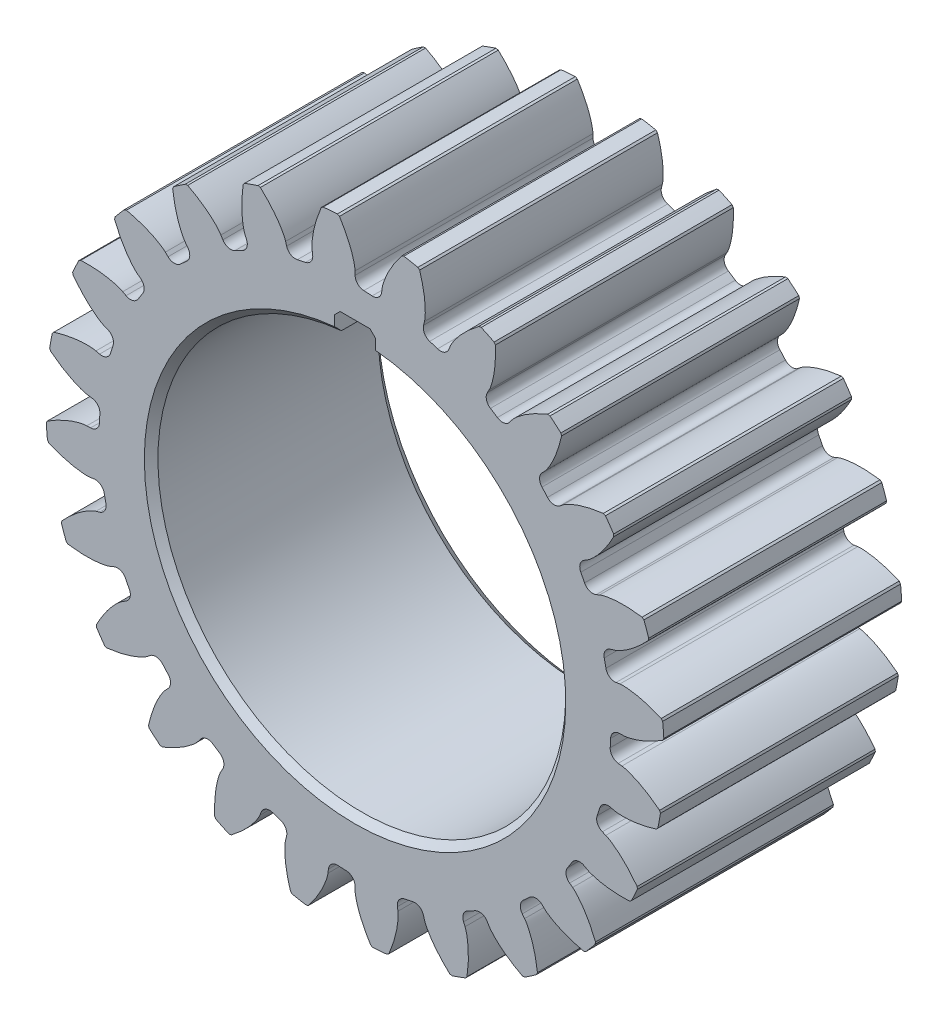
SolidWorks part; units mm, degrees
material "1.6587 (18CrNiMo7-6)"
ref_plane "Front Plane" through (0, 0, 0) normal (0, 0, 1) x (1, 0, 0)
ref_plane "Top Plane" through (0, 0, 0) normal (0, 1, 0) x (1, 0, 0)
ref_plane "Right Plane" through (0, 0, 0) normal (1, 0, 0) x (0, 0, -1)
sketch "Sketch1" plane through (0, 0, 0) normal (0, 0, 1) x (1, 0, 0)
  circle A0 centre (0, 0) radius 42 construction
  circle A1 centre (0, 0) radius 37.625
  dimension "D1" = 84
  dimension "D2" = 4.375
extrude "Boss-Extrude1" add sketch "Sketch1" along normal blind 35
sketch "Sketch2" plane through (0, 0, 0) normal (0, 0, 1) x (1, 0, 0)
  line L0 (39.4671, 0) -> (38.9123, -0.0082)
  line L1 (0, 0) -> (41.9953, 0.626) construction
  line L2 (0, 0) -> (57.5048, 4.6307) construction
  line L3 (38.9585, 6.3154) -> (38.4096, 6.2348)
  circle A0 centre (0, 0) radius 42 construction
  circle A1 centre (0, 0) radius 37.625 construction
  arc A2 (37.6028, -1.2924) -> (36.9114, 7.2929) centre (0, 0) ccw
  arc A3 (45.4365, 2.4027) -> (45.2355, 4.899) centre (0, 0) ccw
  arc A4 (38.9123, -0.0082) -> (37.6028, -1.2924) centre (38.932, -1.3381) ccw
  arc A5 (38.4096, 6.2348) -> (36.9114, 7.2929) centre (38.2162, 7.5506) cw
  circle A6 centre (0, 0) radius 45.5 construction
  spline S0 degree 4 poles (39.4671, 0) (39.4814, 0.0002) (39.5215, 0.0015) (39.5972, 0.0064) (39.7206, 0.0182) (39.8775, 0.0385) (40.0797, 0.071) (40.3172, 0.1173) (40.5771, 0.1764) (40.8586, 0.2496) (41.1382, 0.3305) (41.4158, 0.4184) (41.691, 0.5126) (42.0229, 0.6344) (42.4185, 0.7911) (42.8771, 0.9898) (43.3926, 1.2333) (43.9124, 1.5007) (44.4193, 1.7795) (44.9256, 2.0792) (45.4112, 2.3818) (45.9092, 2.7142) (46.3655, 3.0302) (46.869, 3.4039) (47.2732, 3.7113) (47.7975, 4.1375) (48.1046, 4.3953) (48.4608, 4.7041) (48.6173, 4.845) (48.7137, 4.9316) knots 0 0 0 0 0 0.005377 0.015084 0.028532 0.04661 0.064855 0.092111 0.119476 0.146842 0.174209 0.201575 0.228941 0.256307 0.307035 0.361767 0.4165 0.471232 0.525964 0.580697 0.635429 0.690161 0.744894 0.799626 0.854358 0.909091 0.954545 1 1 1 1 1 construction
  spline S1 degree 4 poles (39.4671, 0) (39.4814, 0.0002) (39.5215, 0.0015) (39.5972, 0.0064) (39.7206, 0.0182) (39.8775, 0.0385) (40.0797, 0.071) (40.3172, 0.1173) (40.5771, 0.1764) (40.8586, 0.2496) (41.1382, 0.3305) (41.4158, 0.4184) (41.691, 0.5126) (42.0229, 0.6344) (42.4185, 0.7911) (42.8771, 0.9898) (43.3926, 1.2333) (43.9124, 1.5007) (44.4193, 1.7795) (44.8682, 2.0452) (45.1794, 2.2376) (45.3694, 2.3592) (45.4365, 2.4027) knots 0 0 0 0 0 0.005377 0.015084 0.028532 0.04661 0.064855 0.092111 0.119476 0.146842 0.174209 0.201575 0.228941 0.256307 0.307035 0.361767 0.4165 0.471232 0.525964 0.580697 0.61062 0.61062 0.61062 0.61062 0.61062
  spline S2 degree 4 poles (38.9585, 6.3154) (38.9727, 6.3175) (39.0125, 6.3227) (39.088, 6.3299) (39.2117, 6.3381) (39.3698, 6.3431) (39.5746, 6.3433) (39.8164, 6.3357) (40.0824, 6.319) (40.372, 6.2918) (40.6609, 6.2566) (40.949, 6.2142) (41.2358, 6.1653) (41.5829, 6.0982) (41.9985, 6.0068) (42.483, 5.8841) (43.0308, 5.7262) (43.5867, 5.5454) (44.1317, 5.3513) (44.6173, 5.1608) (44.9553, 5.0207) (45.1622, 4.9311) (45.2355, 4.899) knots 0 0 0 0 0 0.005377 0.015084 0.028532 0.04661 0.064855 0.092111 0.119476 0.146842 0.174209 0.201575 0.228941 0.256307 0.307035 0.361767 0.4165 0.471232 0.525964 0.580697 0.61062 0.61062 0.61062 0.61062 0.61062
  dimension "D1" = 84
  dimension "D3" = 2.66
  dimension "D4" = 3.75
  dimension "D2" = 3.5
extrude "Boss-Extrude2" add sketch "Sketch2" along normal blind 35
chamfer "Chamfer1" distance 0.2 2 edges at (45.4365, 2.4027, 17.5) (45.2355, 4.899, 17.5)
pattern_circular "CirPattern1" count 24 over 360 about axis through (0, 0, 35) along (0, 0, -1) of "Boss-Extrude2", "Chamfer1"
sketch "Sketch3" plane through (0, 0, 0) normal (0, 0, 1) x (1, 0, 0)
  line L0 (0, 0) -> (0, 33.2) construction
  line L1 (3, 29.8496) -> (3, 33.2)
  line L2 (-3, 29.8496) -> (-3, 33.2)
  line L4 (3, 33.2) -> (-3, 33.2)
  line L5 (3, 0) -> (3, 33.2) construction
  line L6 (-3, 0) -> (-3, 33.2) construction
  arc A0 (-3, 29.8496) -> (3, 29.8496) centre (0, 0) ccw
  dimension "D1" = 60
  dimension "D2" = 33.2
  dimension "D3" = 3
  dimension "D4" = 3
extrude "Cut-Extrude1" cut sketch "Sketch3" along normal blind 35
chamfer "Chamfer2" distance 1 1 edges at (0, -30, 35)
chamfer "Chamfer3" distance 1.6 1 edges at (0, -30, 0)
chamfer "Chamfer4" distance 0.8 2 edges at (3, 33.2, 17.5) (-3, 33.2, 17.5)
